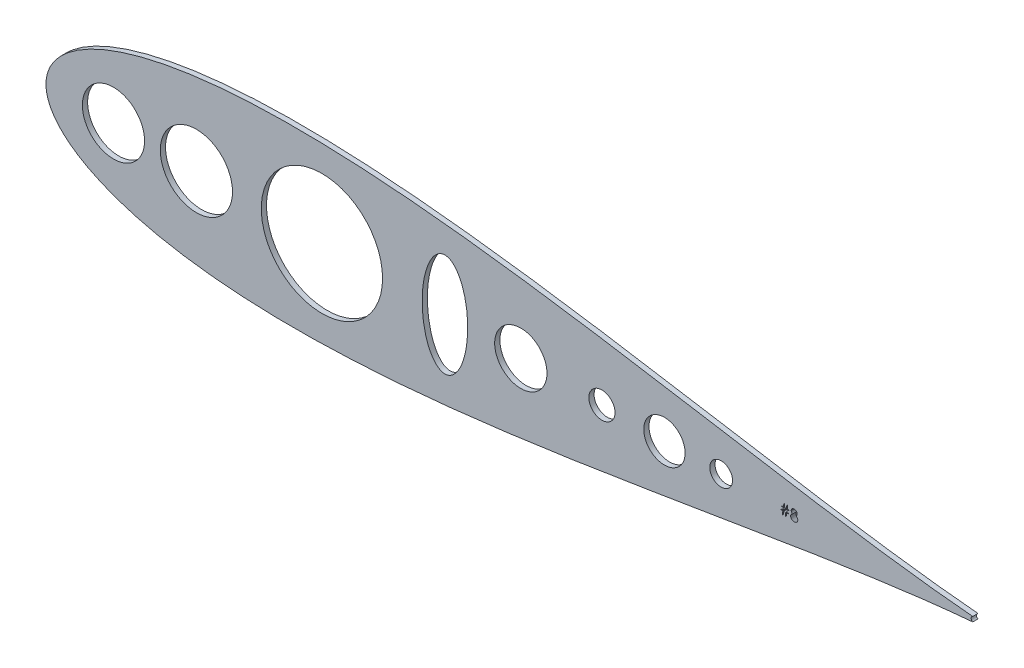
SolidWorks part; units mm, degrees
ref_plane "Front Plane" through (0, 0, 0) normal (0, 0, 1) x (1, 0, 0)
ref_plane "Top Plane" through (0, 0, 0) normal (0, 1, 0) x (1, 0, 0)
ref_plane "Right Plane" through (0, 0, 0) normal (1, 0, 0) x (0, 0, -1)
sketch "Sketch2" plane through (0, 0, 0) normal (0, 0, 1) x (1, 0, 0)
  line L0 (694.3768, 545.3653) -> (694.3768, 545.0397)
  line L1 (694.3768, 545.0397) -> (693.406, 545.0397)
  line L2 (693.406, 545.0397) -> (693.1424, 543.2812)
  line L3 (693.1424, 543.2812) -> (692.7486, 543.2812)
  line L4 (692.7486, 543.2812) -> (693.0121, 545.0397)
  line L5 (693.0121, 545.0397) -> (691.9731, 545.0397)
  line L6 (691.9731, 545.0397) -> (691.7096, 543.2812)
  line L7 (691.7096, 543.2812) -> (691.3158, 543.2812)
  line L8 (691.3158, 543.2812) -> (691.5793, 545.0397)
  line L9 (691.5793, 545.0397) -> (690.7296, 545.0397)
  line L10 (690.7296, 545.0397) -> (690.7296, 545.3653)
  line L11 (690.7296, 545.3653) -> (691.6282, 545.3653)
  line L12 (691.6282, 545.3653) -> (691.8042, 546.5376)
  line L13 (691.8042, 546.5376) -> (690.8599, 546.5376)
  line L14 (690.8599, 546.5376) -> (690.8599, 546.8632)
  line L15 (690.8599, 546.8632) -> (691.8531, 546.8632)
  line L16 (691.8531, 546.8632) -> (692.0973, 548.4915)
  line L17 (692.0973, 548.4915) -> (692.4901, 548.4915)
  line L18 (692.4901, 548.4915) -> (692.2459, 546.8632)
  line L19 (692.2459, 546.8632) -> (693.2859, 546.8632)
  line L20 (693.2859, 546.8632) -> (693.5301, 548.4915)
  line L21 (693.5301, 548.4915) -> (693.9229, 548.4915)
  line L22 (693.9229, 548.4915) -> (693.6787, 546.8632)
  line L23 (693.6787, 546.8632) -> (694.507, 546.8632)
  line L24 (694.507, 546.8632) -> (694.507, 546.5376)
  line L25 (694.507, 546.5376) -> (693.6298, 546.5376)
  line L26 (693.6298, 546.5376) -> (693.4548, 545.3653)
  line L27 (693.4548, 545.3653) -> (694.3768, 545.3653)
  line L28 (693.237, 546.5376) -> (692.197, 546.5376)
  line L29 (692.197, 546.5376) -> (692.022, 545.3653)
  line L30 (692.022, 545.3653) -> (693.061, 545.3653)
  line L31 (693.061, 545.3653) -> (693.237, 546.5376)
  line L32 (697.8235, 546.1112) -> (697.9476, 546.0451)
  line L33 (697.9476, 546.0451) -> (698.0626, 545.9769)
  line L34 (698.0626, 545.9769) -> (698.1685, 545.9057)
  line L35 (698.1685, 545.9057) -> (698.2662, 545.8334)
  line L36 (698.2662, 545.8334) -> (698.3557, 545.7581)
  line L37 (698.3557, 545.7581) -> (698.4361, 545.6797)
  line L38 (698.4361, 545.6797) -> (698.5073, 545.6004)
  line L39 (698.5073, 545.6004) -> (698.5704, 545.5179)
  line L40 (698.5704, 545.5179) -> (698.6254, 545.4335)
  line L41 (698.6254, 545.4335) -> (698.6732, 545.346)
  line L42 (698.6732, 545.346) -> (698.7139, 545.2554)
  line L43 (698.7139, 545.2554) -> (698.7465, 545.1628)
  line L44 (698.7465, 545.1628) -> (698.7729, 545.0661)
  line L45 (698.7729, 545.0661) -> (698.7913, 544.9674)
  line L46 (698.7913, 544.9674) -> (698.8014, 544.8656)
  line L47 (698.8014, 544.8656) -> (698.8055, 544.7608)
  line L48 (698.8055, 544.7608) -> (698.7994, 544.6143)
  line L49 (698.7994, 544.6143) -> (698.7811, 544.4718)
  line L50 (698.7811, 544.4718) -> (698.7516, 544.3334)
  line L51 (698.7516, 544.3334) -> (698.7098, 544.2001)
  line L52 (698.7098, 544.2001) -> (698.6549, 544.0699)
  line L53 (698.6549, 544.0699) -> (698.5887, 543.9457)
  line L54 (698.5887, 543.9457) -> (698.5114, 543.8246)
  line L55 (698.5114, 543.8246) -> (698.4208, 543.7086)
  line L56 (698.4208, 543.7086) -> (698.2967, 543.5783)
  line L57 (698.2967, 543.5783) -> (698.1603, 543.4644)
  line L58 (698.1603, 543.4644) -> (698.0107, 543.3687)
  line L59 (698.0107, 543.3687) -> (697.8479, 543.2904)
  line L60 (697.8479, 543.2904) -> (697.6729, 543.2293)
  line L61 (697.6729, 543.2293) -> (697.4856, 543.1855)
  line L62 (697.4856, 543.1855) -> (697.2852, 543.1601)
  line L63 (697.2852, 543.1601) -> (697.0725, 543.1509)
  line L64 (697.0725, 543.1509) -> (696.8679, 543.1591)
  line L65 (696.8679, 543.1591) -> (696.6756, 543.1815)
  line L66 (696.6756, 543.1815) -> (696.4955, 543.2201)
  line L67 (696.4955, 543.2201) -> (696.3296, 543.2731)
  line L68 (696.3296, 543.2731) -> (696.1749, 543.3423)
  line L69 (696.1749, 543.3423) -> (696.0345, 543.4267)
  line L70 (696.0345, 543.4267) -> (695.9063, 543.5254)
  line L71 (695.9063, 543.5254) -> (695.7903, 543.6404)
  line L72 (695.7903, 543.6404) -> (695.6875, 543.7646)
  line L73 (695.6875, 543.7646) -> (695.599, 543.8918)
  line L74 (695.599, 543.8918) -> (695.5247, 544.022)
  line L75 (695.5247, 544.022) -> (695.4626, 544.1553)
  line L76 (695.4626, 544.1553) -> (695.4148, 544.2917)
  line L77 (695.4148, 544.2917) -> (695.3812, 544.4311)
  line L78 (695.3812, 544.4311) -> (695.3608, 544.5736)
  line L79 (695.3608, 544.5736) -> (695.3537, 544.7191)
  line L80 (695.3537, 544.7191) -> (695.3578, 544.826)
  line L81 (695.3578, 544.826) -> (695.369, 544.9298)
  line L82 (695.369, 544.9298) -> (695.3873, 545.0305)
  line L83 (695.3873, 545.0305) -> (695.4127, 545.1292)
  line L84 (695.4127, 545.1292) -> (695.4463, 545.2249)
  line L85 (695.4463, 545.2249) -> (695.487, 545.3175)
  line L86 (695.487, 545.3175) -> (695.5348, 545.408)
  line L87 (695.5348, 545.408) -> (695.5898, 545.4956)
  line L88 (695.5898, 545.4956) -> (695.6539, 545.581)
  line L89 (695.6539, 545.581) -> (695.7262, 545.6635)
  line L90 (695.7262, 545.6635) -> (695.8086, 545.7439)
  line L91 (695.8086, 545.7439) -> (695.9002, 545.8222)
  line L92 (695.9002, 545.8222) -> (695.9999, 545.8985)
  line L93 (695.9999, 545.8985) -> (696.1098, 545.9718)
  line L94 (696.1098, 545.9718) -> (696.2279, 546.043)
  line L95 (696.2279, 546.043) -> (696.3561, 546.1112)
  line L96 (696.3561, 546.1112) -> (696.1821, 546.212)
  line L97 (696.1821, 546.212) -> (696.0314, 546.3249)
  line L98 (696.0314, 546.3249) -> (695.9042, 546.4481)
  line L99 (695.9042, 546.4481) -> (695.7994, 546.5834)
  line L100 (695.7994, 546.5834) -> (695.718, 546.7269)
  line L101 (695.718, 546.7269) -> (695.661, 546.8755)
  line L102 (695.661, 546.8755) -> (695.6254, 547.0291)
  line L103 (695.6254, 547.0291) -> (695.6142, 547.1879)
  line L104 (695.6142, 547.1879) -> (695.6264, 547.3497)
  line L105 (695.6264, 547.3497) -> (695.6631, 547.5094)
  line L106 (695.6631, 547.5094) -> (695.7251, 547.6682)
  line L107 (695.7251, 547.6682) -> (695.8106, 547.8239)
  line L108 (695.8106, 547.8239) -> (695.9185, 547.9714)
  line L109 (695.9185, 547.9714) -> (696.0447, 548.1017)
  line L110 (696.0447, 548.1017) -> (696.1892, 548.2157)
  line L111 (696.1892, 548.2157) -> (696.353, 548.3134)
  line L112 (696.353, 548.3134) -> (696.5301, 548.3917)
  line L113 (696.5301, 548.3917) -> (696.7143, 548.4467)
  line L114 (696.7143, 548.4467) -> (696.9046, 548.4803)
  line L115 (696.9046, 548.4803) -> (697.103, 548.4915)
  line L116 (697.103, 548.4915) -> (697.2964, 548.4803)
  line L117 (697.2964, 548.4803) -> (697.4816, 548.4467)
  line L118 (697.4816, 548.4467) -> (697.6597, 548.3897)
  line L119 (697.6597, 548.3897) -> (697.8306, 548.3113)
  line L120 (697.8306, 548.3113) -> (697.9894, 548.2136)
  line L121 (697.9894, 548.2136) -> (698.1288, 548.0986)
  line L122 (698.1288, 548.0986) -> (698.2509, 547.9684)
  line L123 (698.2509, 547.9684) -> (698.3547, 547.8219)
  line L124 (698.3547, 547.8219) -> (698.4381, 547.6662)
  line L125 (698.4381, 547.6662) -> (698.4972, 547.5054)
  line L126 (698.4972, 547.5054) -> (698.5328, 547.3415)
  line L127 (698.5328, 547.3415) -> (698.545, 547.1736)
  line L128 (698.545, 547.1736) -> (698.5338, 547.0088)
  line L129 (698.5338, 547.0088) -> (698.5002, 546.8531)
  line L130 (698.5002, 546.8531) -> (698.4432, 546.7065)
  line L131 (698.4432, 546.7065) -> (698.3649, 546.5692)
  line L132 (698.3649, 546.5692) -> (698.2631, 546.4409)
  line L133 (698.2631, 546.4409) -> (698.14, 546.3229)
  line L134 (698.14, 546.3229) -> (697.9924, 546.212)
  line L135 (697.9924, 546.212) -> (697.8235, 546.1112)
  line L136 (697.0776, 547.9704) -> (696.9707, 547.9664)
  line L137 (696.9707, 547.9664) -> (696.869, 547.9562)
  line L138 (696.869, 547.9562) -> (696.7723, 547.9379)
  line L139 (696.7723, 547.9379) -> (696.6797, 547.9124)
  line L140 (696.6797, 547.9124) -> (696.5911, 547.8788)
  line L141 (696.5911, 547.8788) -> (696.5087, 547.8392)
  line L142 (696.5087, 547.8392) -> (696.4304, 547.7913)
  line L143 (696.4304, 547.7913) -> (696.3561, 547.7364)
  line L144 (696.3561, 547.7364) -> (696.2889, 547.6763)
  line L145 (696.2889, 547.6763) -> (696.2309, 547.6143)
  line L146 (696.2309, 547.6143) -> (696.1821, 547.5491)
  line L147 (696.1821, 547.5491) -> (696.1414, 547.4809)
  line L148 (696.1414, 547.4809) -> (696.1108, 547.4097)
  line L149 (696.1108, 547.4097) -> (696.0884, 547.3364)
  line L150 (696.0884, 547.3364) -> (696.0742, 547.2601)
  line L151 (696.0742, 547.2601) -> (696.0701, 547.1807)
  line L152 (696.0701, 547.1807) -> (696.0752, 547.1014)
  line L153 (696.0752, 547.1014) -> (696.0895, 547.0251)
  line L154 (696.0895, 547.0251) -> (696.1129, 546.9497)
  line L155 (696.1129, 546.9497) -> (696.1475, 546.8765)
  line L156 (696.1475, 546.8765) -> (696.1902, 546.8052)
  line L157 (696.1902, 546.8052) -> (696.2431, 546.735)
  line L158 (696.2431, 546.735) -> (696.3052, 546.6679)
  line L159 (696.3052, 546.6679) -> (696.3774, 546.6017)
  line L160 (696.3774, 546.6017) -> (696.4558, 546.5407)
  line L161 (696.4558, 546.5407) -> (696.5382, 546.4877)
  line L162 (696.5382, 546.4877) -> (696.6227, 546.444)
  line L163 (696.6227, 546.444) -> (696.7112, 546.4074)
  line L164 (696.7112, 546.4074) -> (696.8028, 546.3789)
  line L165 (696.8028, 546.3789) -> (696.8974, 546.3585)
  line L166 (696.8974, 546.3585) -> (696.9951, 546.3463)
  line L167 (696.9951, 546.3463) -> (697.0959, 546.3422)
  line L168 (697.0959, 546.3422) -> (697.2251, 546.3493)
  line L169 (697.2251, 546.3493) -> (697.3513, 546.3717)
  line L170 (697.3513, 546.3717) -> (697.4734, 546.4084)
  line L171 (697.4734, 546.4084) -> (697.5925, 546.4592)
  line L172 (697.5925, 546.4592) -> (697.7034, 546.5234)
  line L173 (697.7034, 546.5234) -> (697.8011, 546.5987)
  line L174 (697.8011, 546.5987) -> (697.8856, 546.6841)
  line L175 (697.8856, 546.6841) -> (697.9578, 546.7808)
  line L176 (697.9578, 546.7808) -> (698.0148, 546.8836)
  line L177 (698.0148, 546.8836) -> (698.0565, 546.9854)
  line L178 (698.0565, 546.9854) -> (698.081, 547.0881)
  line L179 (698.081, 547.0881) -> (698.0891, 547.1909)
  line L180 (698.0891, 547.1909) -> (698.085, 547.2632)
  line L181 (698.085, 547.2632) -> (698.0728, 547.3334)
  line L182 (698.0728, 547.3334) -> (698.0525, 547.4016)
  line L183 (698.0525, 547.4016) -> (698.024, 547.4698)
  line L184 (698.024, 547.4698) -> (697.9873, 547.5359)
  line L185 (697.9873, 547.5359) -> (697.9436, 547.6)
  line L186 (697.9436, 547.6) -> (697.8907, 547.6631)
  line L187 (697.8907, 547.6631) -> (697.8296, 547.7252)
  line L188 (697.8296, 547.7252) -> (697.7614, 547.7822)
  line L189 (697.7614, 547.7822) -> (697.6861, 547.832)
  line L190 (697.6861, 547.832) -> (697.6027, 547.8748)
  line L191 (697.6027, 547.8748) -> (697.5121, 547.9094)
  line L192 (697.5121, 547.9094) -> (697.4144, 547.9358)
  line L193 (697.4144, 547.9358) -> (697.3096, 547.9552)
  line L194 (697.3096, 547.9552) -> (697.1977, 547.9664)
  line L195 (697.1977, 547.9664) -> (697.0776, 547.9704)
  line L196 (697.1071, 545.8212) -> (696.9717, 545.8161)
  line L197 (696.9717, 545.8161) -> (696.8425, 545.7998)
  line L198 (696.8425, 545.7998) -> (696.7183, 545.7744)
  line L199 (696.7183, 545.7744) -> (696.6003, 545.7378)
  line L200 (696.6003, 545.7378) -> (696.4873, 545.6899)
  line L201 (696.4873, 545.6899) -> (696.3795, 545.6319)
  line L202 (696.3795, 545.6319) -> (696.2777, 545.5637)
  line L203 (696.2777, 545.5637) -> (696.1821, 545.4854)
  line L204 (696.1821, 545.4854) -> (696.0945, 545.3999)
  line L205 (696.0945, 545.3999) -> (696.0192, 545.3114)
  line L206 (696.0192, 545.3114) -> (695.9551, 545.2188)
  line L207 (695.9551, 545.2188) -> (695.9032, 545.1231)
  line L208 (695.9032, 545.1231) -> (695.8615, 545.0234)
  line L209 (695.8615, 545.0234) -> (695.833, 544.9206)
  line L210 (695.833, 544.9206) -> (695.8157, 544.8137)
  line L211 (695.8157, 544.8137) -> (695.8096, 544.7038)
  line L212 (695.8096, 544.7038) -> (695.8198, 544.5675)
  line L213 (695.8198, 544.5675) -> (695.8493, 544.4362)
  line L214 (695.8493, 544.4362) -> (695.8992, 544.307)
  line L215 (695.8992, 544.307) -> (695.9684, 544.1828)
  line L216 (695.9684, 544.1828) -> (696.0559, 544.0668)
  line L217 (696.0559, 544.0668) -> (696.1597, 543.9661)
  line L218 (696.1597, 543.9661) -> (696.2787, 543.8775)
  line L219 (696.2787, 543.8775) -> (696.4141, 543.8043)
  line L220 (696.4141, 543.8043) -> (696.5637, 543.7463)
  line L221 (696.5637, 543.7463) -> (696.7234, 543.7055)
  line L222 (696.7234, 543.7055) -> (696.8954, 543.6801)
  line L223 (696.8954, 543.6801) -> (697.0776, 543.672)
  line L224 (697.0776, 543.672) -> (697.22, 543.6771)
  line L225 (697.22, 543.6771) -> (697.3544, 543.6923)
  line L226 (697.3544, 543.6923) -> (697.4816, 543.7178)
  line L227 (697.4816, 543.7178) -> (697.6006, 543.7534)
  line L228 (697.6006, 543.7534) -> (697.7126, 543.7982)
  line L229 (697.7126, 543.7982) -> (697.8174, 543.8541)
  line L230 (697.8174, 543.8541) -> (697.9151, 543.9192)
  line L231 (697.9151, 543.9192) -> (698.0046, 543.9956)
  line L232 (698.0046, 543.9956) -> (698.085, 544.078)
  line L233 (698.085, 544.078) -> (698.1552, 544.1645)
  line L234 (698.1552, 544.1645) -> (698.2153, 544.254)
  line L235 (698.2153, 544.254) -> (698.2631, 544.3467)
  line L236 (698.2631, 544.3467) -> (698.3008, 544.4423)
  line L237 (698.3008, 544.4423) -> (698.3282, 544.542)
  line L238 (698.3282, 544.542) -> (698.3445, 544.6448)
  line L239 (698.3445, 544.6448) -> (698.3496, 544.7517)
  line L240 (698.3496, 544.7517) -> (698.3435, 544.8555)
  line L241 (698.3435, 544.8555) -> (698.3272, 544.9552)
  line L242 (698.3272, 544.9552) -> (698.2987, 545.0529)
  line L243 (698.2987, 545.0529) -> (698.259, 545.1475)
  line L244 (698.259, 545.1475) -> (698.2071, 545.2391)
  line L245 (698.2071, 545.2391) -> (698.1451, 545.3276)
  line L246 (698.1451, 545.3276) -> (698.0708, 545.4131)
  line L247 (698.0708, 545.4131) -> (697.9853, 545.4956)
  line L248 (697.9853, 545.4956) -> (697.8917, 545.5719)
  line L249 (697.8917, 545.5719) -> (697.794, 545.638)
  line L250 (697.794, 545.638) -> (697.6912, 545.694)
  line L251 (697.6912, 545.694) -> (697.5833, 545.7398)
  line L252 (697.5833, 545.7398) -> (697.4714, 545.7754)
  line L253 (697.4714, 545.7754) -> (697.3544, 545.8008)
  line L254 (697.3544, 545.8008) -> (697.2333, 545.8161)
  line L255 (697.2333, 545.8161) -> (697.1071, 545.8212)
  circle A0 centre (406.8977, 545.5348) radius 17.526
  circle A1 centre (366.6463, 545.5348) radius 15.0914
  circle A2 centre (564.3777, 545.5348) radius 12.7
  circle A3 centre (603.7477, 545.5348) radius 6.35
  circle A4 centre (467.8255, 545.5348) radius 29.4326
  circle A5 centre (634.0834, 545.5348) radius 10.0345
  circle A6 centre (661.6144, 545.5348) radius 5.5299
  arc A7 (783.748, 546.6896) -> (783.7459, 544.3797) centre (784.2108, 545.5343) ccw
  ellipse E0 centre (527.5368, 545.5348) end of major axis (527.5368, 520.5466) minor radius 11.0619
  spline S0 degree 3 poles (783.748, 546.6896) (783.5679, 546.7048) (781.0177, 546.921) (775.8156, 547.4018) (767.8244, 548.2331) (758.9644, 549.2532) (749.2688, 550.4682) (738.7829, 551.8793) (727.5521, 553.4834) (715.6249, 555.2721) (703.0521, 557.2329) (689.8862, 559.3481) (676.1817, 561.5959) (661.9946, 563.9503) (647.3823, 566.3818) (632.4035, 568.8573) (617.118, 571.3408) (601.5869, 573.7944) (585.8723, 576.1779) (570.0376, 578.4505) (554.1471, 580.5706) (538.2663, 582.4969) (522.462, 584.1888) (506.8018, 585.6072) (491.3548, 586.7151) (476.191, 587.4785) (461.3816, 587.8664) (446.999, 587.852) (433.1165, 587.4124) (419.8088, 586.5305) (407.1517, 585.1934) (395.2225, 583.395) (384.1009, 581.1349) (373.8692, 578.4205) (364.6137, 575.2677) (356.4268, 571.7046) (349.408, 567.7785) (343.6622, 563.569) (339.286, 559.2135) (336.3232, 554.9424) (334.6711, 551.0891) (334.0039, 547.9979) (333.852, 545.5348) (334.0039, 543.0716) (334.6711, 539.9805) (336.3232, 536.1271) (339.286, 531.856) (343.6622, 527.5006) (349.408, 523.291) (356.4268, 519.3649) (364.6137, 515.8019) (373.8692, 512.6491) (384.1009, 509.9347) (395.2225, 507.6745) (407.1517, 505.8762) (419.8088, 504.5391) (433.1165, 503.6571) (446.999, 503.2175) (461.3816, 503.2031) (476.191, 503.5911) (491.3548, 504.3544) (506.8018, 505.4624) (522.462, 506.8808) (538.2663, 508.5726) (554.1471, 510.4989) (570.0376, 512.619) (585.8723, 514.8916) (601.5869, 517.2752) (617.118, 519.7287) (632.4035, 522.2123) (647.3823, 524.6877) (661.9946, 527.1192) (676.1817, 529.4737) (689.8862, 531.7215) (703.0521, 533.8367) (715.6249, 535.7974) (727.5521, 537.5862) (738.7829, 539.1903) (749.2688, 540.6014) (758.9644, 541.8164) (767.8244, 542.8364) (775.8156, 543.6677) (781.017, 544.1485) (783.5665, 544.3646) (783.7459, 544.3797) knots 0.020718 0.020718 0.020718 0.020718 0.021271 0.028553 0.036781 0.04592 0.055932 0.066773 0.078397 0.090755 0.103793 0.117456 0.131686 0.146422 0.1616 0.177156 0.193024 0.209135 0.225421 0.241812 0.258238 0.274629 0.290914 0.307025 0.322893 0.338448 0.353626 0.368361 0.38259 0.396253 0.40929 0.421647 0.43327 0.444109 0.454119 0.463255 0.471479 0.478755 0.485052 0.490344 0.49461 0.497833 0.5 0.502167 0.50539 0.509656 0.514948 0.521245 0.528521 0.536745 0.545881 0.555891 0.56673 0.578353 0.59071 0.603747 0.61741 0.631639 0.646374 0.661552 0.677107 0.692975 0.709086 0.725371 0.741762 0.758188 0.774579 0.790865 0.806976 0.822844 0.8384 0.853578 0.868314 0.882544 0.896207 0.909245 0.921603 0.933227 0.944068 0.95408 0.963219 0.971447 0.978729 0.97928 0.97928 0.97928 0.97928
extrude "Boss-Extrude1" add sketch "Sketch2" along normal blind 2.54 contours A7 S0 L134 L135 L32 L33 L34 L35 L36 L37 L38 L39 L40 L41 L42 L43 L44 L45 L46 L47 L48 L49 L50 L51 L52 L53 L54 L55 L56 L57 L58 L59 L60 L61 L62 L63 L64 L65 L66 L67 L68 L69 L70 L71 L72 L73 L74 L75 L76 L77
